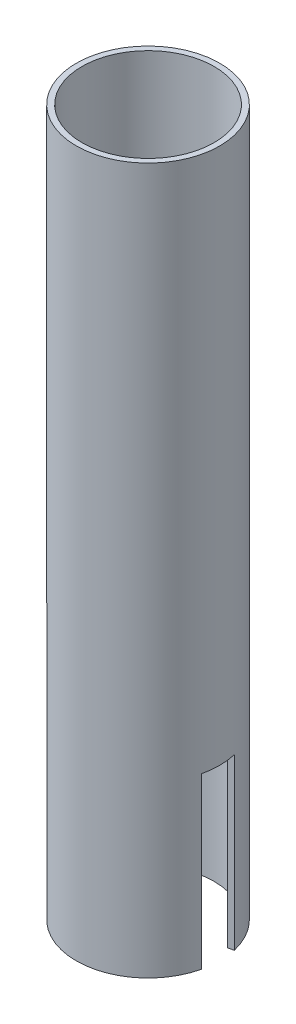
SolidWorks part; units mm, degrees
ref_plane "Front Plane" through (0, 0, 0) normal (0, 0, 1) x (1, 0, 0)
ref_plane "Top Plane" through (0, 0, 0) normal (0, 1, 0) x (1, 0, 0)
ref_plane "Right Plane" through (0, 0, 0) normal (1, 0, 0) x (0, 0, -1)
sketch "Sketch1" plane through (0, 0, 0) normal (0, 1, 0) x (1, 0, 0)
  circle A0 centre (0, 0) radius 25.4
  circle A1 centre (0, 0) radius 23.4
  dimension "Outer_Dia" = 50.8
  dimension "Inner_Dia" = 46.8
extrude "Boss-Extrude1" add sketch "Sketch1" along normal mid plane 250
sketch "Sketch3" plane through (0, 0, 0) normal (0, 0, 1) x (1, 0, 0)
  line L0 (-25.4, -125) -> (25.4, -125) construction
  line L1 (1, -65) -> (-1, -65)
  line L2 (1, -65) -> (1, -125)
  line L3 (1, -125) -> (-1, -125)
  line L4 (-1, -65) -> (-1, -125)
  line L5 (1, -65) -> (-1, -125) construction
  line L6 (1, -125) -> (-1, -65) construction
  point P0 (0, -95)
  point P7 (0, 0)
  dimension "D1" = 2
  dimension "D2" = 60
curve "Curve1"
sketch "Sketch4" plane through (0, 0, 0) normal (1, 0, 0) x (0, 0, -1)
  line L0 (-25.4, -125) -> (25.4, -125) construction
  line L1 (1, -65) -> (-1, -65)
  line L2 (1, -65) -> (1, -125)
  line L3 (1, -125) -> (-1, -125)
  line L4 (-1, -65) -> (-1, -125)
  line L5 (1, -65) -> (-1, -125) construction
  line L6 (1, -125) -> (-1, -65) construction
  point P0 (0, -95)
  point P7 (0, 0)
  dimension "D1" = 60
  dimension "D2" = 2
curve "Curve2"
sketch "Sketch2" plane through (0, -125, 0) normal (0, -1, 0) x (1, 0, 0)
  line L0 (-54.8088, 0) -> (54.8088, 0) construction
  line L1 (-24.7197, -5.8393) -> (-22.7732, -5.3795)
  line L2 (0, 41.0316) -> (0, -42.2819) construction
  line L3 (-24.7197, 5.8393) -> (-22.7732, 5.3795)
  line L4 (25.4, 6) -> (-25.4, 6) construction
  line L5 (25.4, 6) -> (25.4, -6) construction
  line L6 (25.4, -6) -> (-25.4, -6) construction
  line L7 (-25.4, 6) -> (-25.4, -6) construction
  line L8 (25.4, 6) -> (-25.4, -6) construction
  line L9 (25.4, -6) -> (-25.4, 6) construction
  line L10 (24.7197, -5.8393) -> (22.7732, -5.3795)
  line L11 (24.7197, 5.8393) -> (22.7732, 5.3795)
  circle A0 centre (0, 0) radius 25.4 construction
  circle A1 centre (0, 0) radius 23.4 construction
  arc A2 (22.7732, -5.3795) -> (22.7732, 5.3795) centre (0, 0) ccw
  circle A3 centre (0, 0) radius 25.4
  arc A4 (24.7197, -5.8393) -> (24.7197, 5.8393) centre (0, 0) ccw
  arc A5 (-24.7197, 5.8393) -> (-24.7197, -5.8393) centre (0, 0) ccw
  arc A7 (-22.7732, 5.3795) -> (-22.7732, -5.3795) centre (0, 0) ccw
  point P3 (0, 0)
  point P15 (0, 0)
  dimension "D1" = 12
  dimension "D2" = 0
extrude "Cut-Extrude1" cut sketch "Sketch2" against normal up to vertex (60 mm away)
